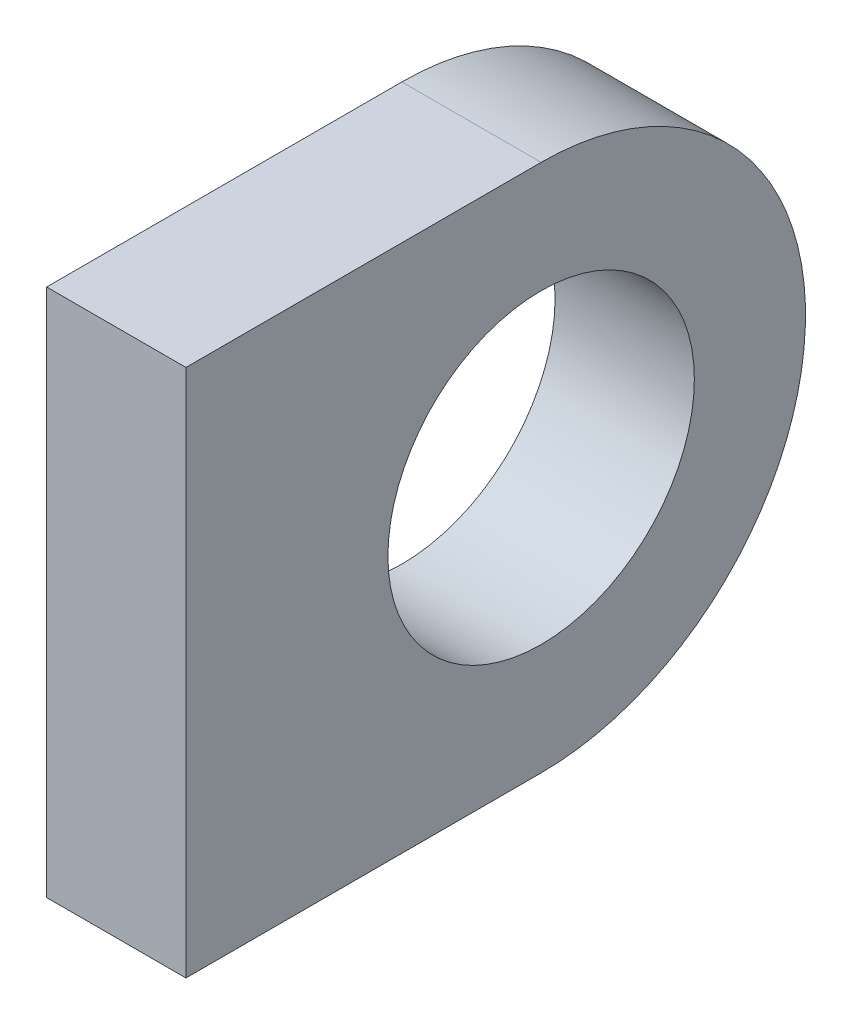
SolidWorks part; units mm, degrees
ref_plane "Front Plane" through (0, 0, 0) normal (0, 0, 1) x (1, 0, 0)
ref_plane "Top Plane" through (0, 0, 0) normal (0, 1, 0) x (1, 0, 0)
ref_plane "Right Plane" through (0, 0, 0) normal (1, 0, 0) x (0, 0, -1)
sketch "Sketch1" plane through (0, 0, 0) normal (1, 0, 0) x (0, 0, -1)
  line L0 (-23.5, 18.9805) -> (0, 18.9805)
  line L1 (0, 0) -> (-23.5, 0) construction
  line L3 (-23.5, -18.9805) -> (0, -18.9805)
  line L4 (-23.5, -18.9805) -> (-23.5, 18.9805)
  arc A0 (0, -18.9805) -> (0, 18.9805) centre (0, 0) ccw
  dimension "D1" = 37.961
  dimension "D2" = 23.5
extrude "Boss-Extrude1" add sketch "Sketch1" along normal blind 10
sketch "Sketch2" plane through (0, 0, 0) normal (-1, 0, 0) x (0, 0, 1)
  circle A0 centre (0, 0) radius 11
  dimension "D1" = 22
extrude "Cut-Extrude1" cut sketch "Sketch2" against normal blind 10
sketch "Sketch3" plane through (0, 18.9805, 0) normal (0, 1, 0) x (1, 0, 0)
  line L1 (0, -23.5) -> (10, -23.5)
  line L2 (0, -23.5) -> (0, -25.5)
  line L3 (0, -25.5) -> (10, -25.5)
  line L4 (10, -23.5) -> (10, -25.5)
  dimension "D1" = 2
  dimension "D2" = 10
extrude "Boss-Extrude2" add sketch "Sketch3" against normal up to surface (37.961 mm away)
